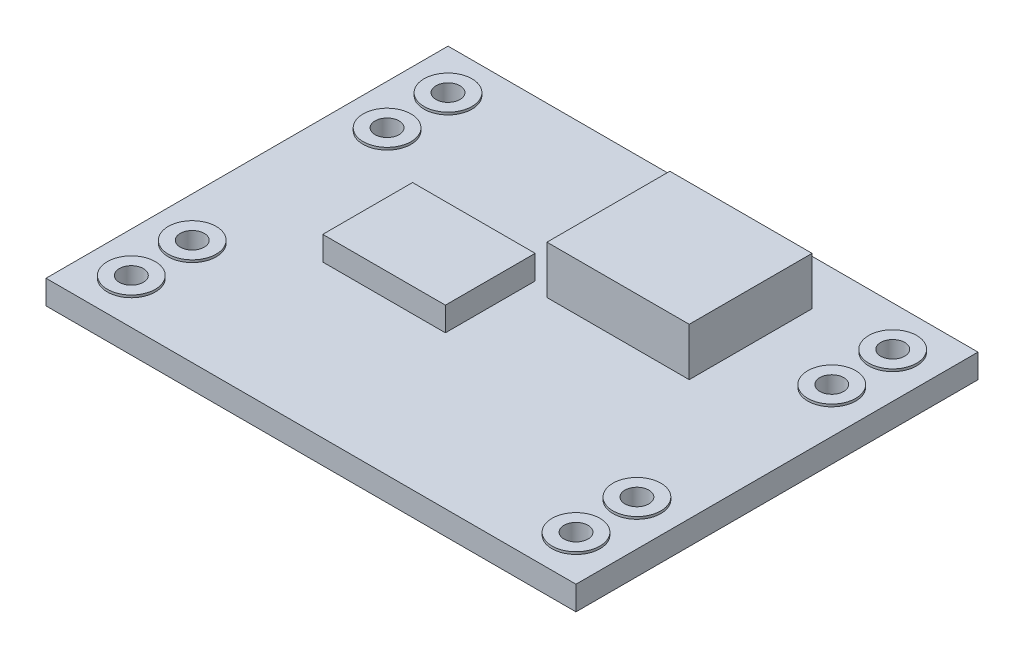
SolidWorks part; units mm, degrees
ref_plane "Спереди" through (0, 0, 0) normal (0, 0, 1) x (1, 0, 0)
ref_plane "Сверху" through (0, 0, 0) normal (0, 1, 0) x (1, 0, 0)
ref_plane "Справа" through (0, 0, 0) normal (1, 0, 0) x (0, 0, -1)
sketch "Sketch1" plane through (0, 0, 0) normal (0, 1, 0) x (1, 0, 0)
  line L1 (0, 0) -> (22.098, 0)
  line L2 (0, 0) -> (0, 16.764)
  line L3 (0, 16.764) -> (22.098, 16.764)
  line L4 (22.098, 0) -> (22.098, 16.764)
  dimension "D1" = 22.098
  dimension "D2" = 16.764
extrude "Boss-Extrude1" add sketch "Sketch1" along normal blind 1
sketch "Sketch2" plane through (0, 0, 0) normal (0, -1, 0) x (1, 0, 0)
  line L0 (0, -16.764) -> (0, 0) construction
  line L1 (22.098, 0) -> (22.098, -16.764) construction
  line L2 (22.098, -16.764) -> (0, -16.764) construction
  line L3 (0, 0) -> (22.098, 0) construction
  circle A0 centre (1.778, -14.984) radius 1
  circle A1 centre (20.32, -14.9858) radius 1
  circle A2 centre (1.778, -12.444) radius 1
  circle A3 centre (20.32, -12.444) radius 1
  circle A4 centre (1.778, -1.78) radius 1
  circle A5 centre (1.778, -4.32) radius 1
  circle A6 centre (20.32, -4.32) radius 1
  circle A7 centre (20.32, -1.78) radius 1
  dimension "D2" = 2
  dimension "D4" = 2
  dimension "D7" = 2.54
  dimension "D8" = 1.78
  dimension "D9" = 2.54
  dimension "D1" = 1.778
  dimension "D3" = 1.778
  dimension "D5" = 1.78
  dimension "D6" = 1.7782
extrude "Boss-Extrude2" add sketch "Sketch2" against normal blind 1.1
sketch "Sketch4" plane through (0, 1.1, 0) normal (0, 1, 0) x (1, 0, 0)
  circle A0 centre (1.778, 14.984) radius 0.5
  circle A1 centre (1.778, 12.444) radius 0.5
  circle A2 centre (1.778, 4.32) radius 0.5
  circle A3 centre (1.778, 1.78) radius 0.5
  circle A4 centre (20.32, 14.9858) radius 0.5
  circle A5 centre (20.32, 12.444) radius 0.5
  circle A6 centre (20.32, 4.32) radius 0.5
  circle A7 centre (20.32, 1.78) radius 0.5
extrude "Cut-Extrude1" cut sketch "Sketch4" against normal blind 1.1
sketch "Sketch5" plane through (0, 1, 0) normal (0, 1, 0) x (1, 0, 0)
  line L1 (17.0731, 14.8708) -> (11.1421, 14.8708)
  line L2 (17.0731, 14.8708) -> (17.0731, 9.7468)
  line L3 (17.0731, 9.7468) -> (11.1421, 9.7468)
  line L4 (11.1421, 14.8708) -> (11.1421, 9.7468)
extrude "Boss-Extrude3" add sketch "Sketch5" along normal blind 2
sketch "Sketch6" plane through (0, 1, 0) normal (0, 1, 0) x (1, 0, 0)
  line L1 (10.2988, 10.0979) -> (5.186, 10.0979)
  line L2 (10.2988, 10.0979) -> (10.2988, 6.355)
  line L3 (10.2988, 6.355) -> (5.186, 6.355)
  line L4 (5.186, 10.0979) -> (5.186, 6.355)
extrude "Boss-Extrude4" add sketch "Sketch6" along normal blind 1
